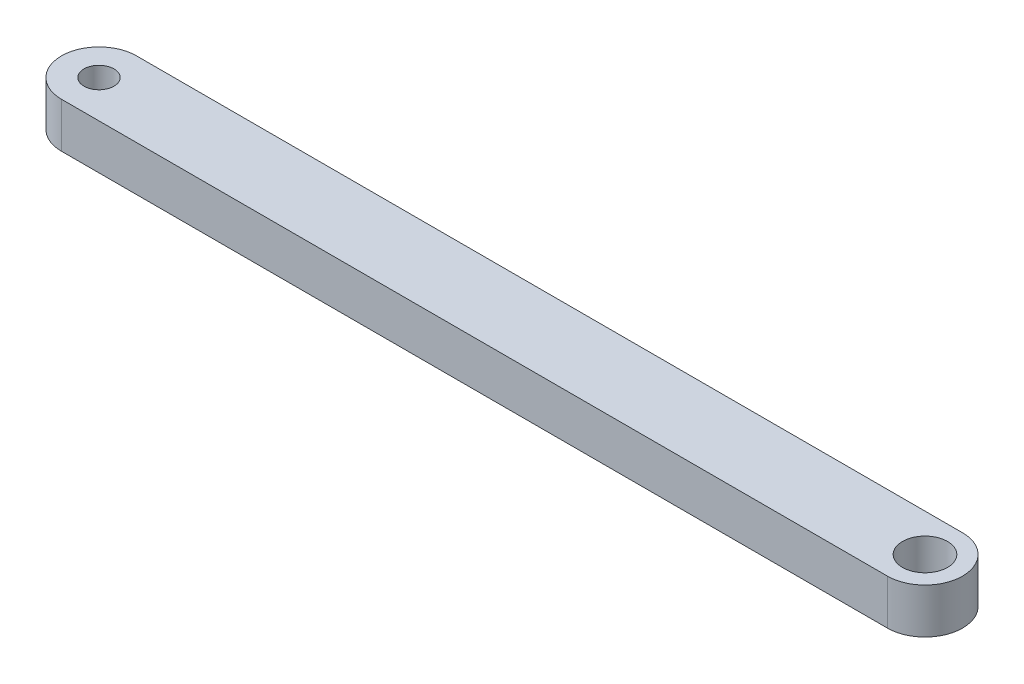
SolidWorks part; units mm, degrees
ref_plane "Front Plane" through (0, 0, 0) normal (0, 0, 1) x (1, 0, 0)
ref_plane "Top Plane" through (0, 0, 0) normal (0, 1, 0) x (1, 0, 0)
ref_plane "Right Plane" through (0, 0, 0) normal (1, 0, 0) x (0, 0, -1)
ref_plane "Plane1" through (0, 0, 0) normal (0, -1, 0) x (1, 0, 0)
sketch "Sketch1" plane through (0, 0, 0) normal (0, -1, 0) x (1, 0, 0)
  line L0 (46, 2.5) -> (-9, 2.5)
  line L1 (-9, -2.5) -> (46, -2.5)
  line L2 (46.727, -3.8369) -> (80.5024, 56.9042) construction
  line L3 (46.0429, -0.0239) -> (48.5752, 4.5302) construction
  line L4 (46, 0) -> (46.0173, -0.0096) construction
  line L5 (46, 0) -> (46.0096, 0.0173) construction
  line L6 (29.6846, 5.6397) -> (46.727, -3.8369) construction
  line L7 (46.0429, -0.0239) -> (44.4093, 0.8845) construction
  line L9 (-10.2659, -8.4497) -> (-2.4903, 5.5338) construction
  arc A0 (-9, 2.5) -> (-9, -2.5) centre (-9, 0) ccw
  arc A1 (46, -2.5) -> (46, 2.5) centre (46, 0) ccw
  circle A2 centre (46, 0) radius 1.5
  circle A3 centre (-9, 0) radius 1
  point P9 (-11.5, 0)
  point P10 (48.5, 0)
  point P22 (53.2116, 8.66)
  dimension "D1" = 2
  dimension "D2" = 3
  dimension "D3" = 2.5
  dimension "D4" = 55
  dimension "D5" = 9
extrude "Boss-Extrude1" add sketch "Sketch1" against normal blind 3
